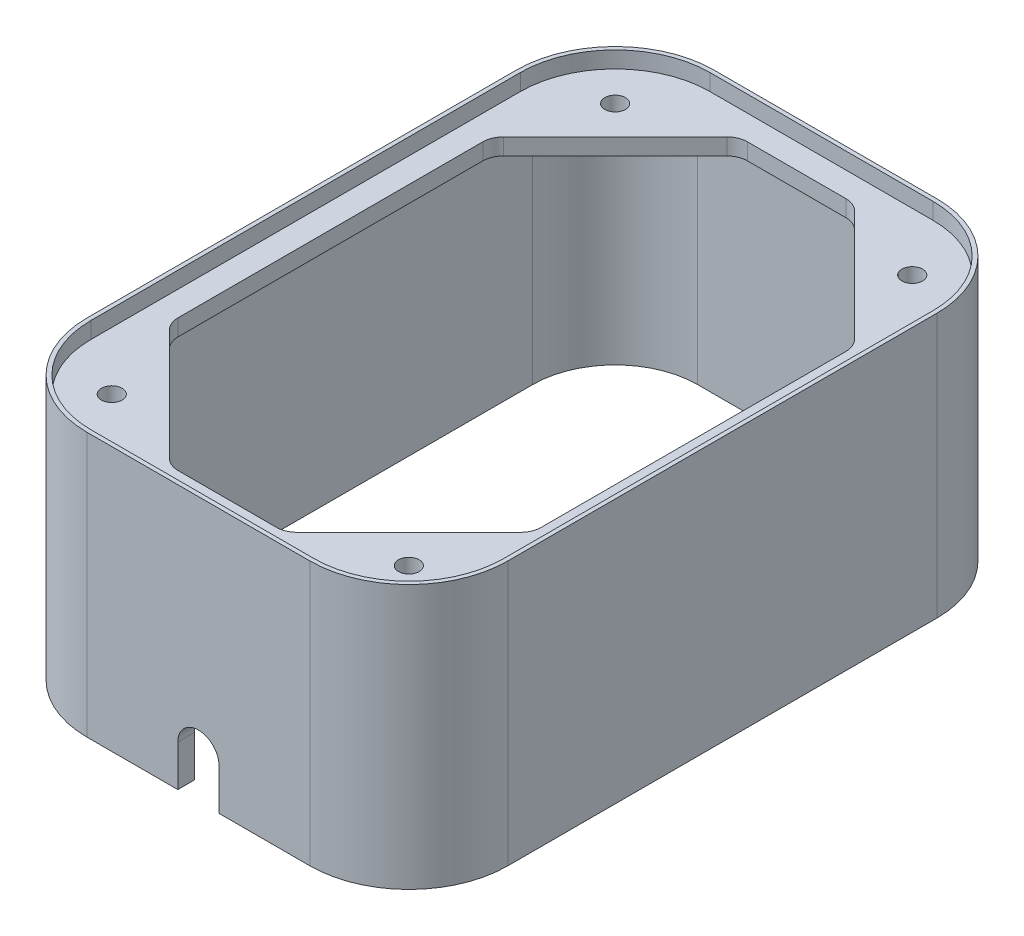
SolidWorks part; units mm, degrees
ref_plane "Front Plane" through (0, 0, 0) normal (0, 0, 1) x (1, 0, 0)
ref_plane "Top Plane" through (0, 0, 0) normal (0, 1, 0) x (1, 0, 0)
ref_plane "Right Plane" through (0, 0, 0) normal (1, 0, 0) x (0, 0, -1)
sketch "Sketch1" plane through (0, 0, 0) normal (0, 1, 0) x (1, 0, 0)
  line L0 (98.6595, -61) -> (-159.6366, -61) construction
  line L1 (-27, -75) -> (27, -75) construction
  line L2 (-50, -52) -> (-50, 52) construction
  line L3 (-27, 75) -> (27, 75) construction
  line L4 (50, -52) -> (50, 52) construction
  line L5 (-50, -75) -> (50, 75) construction
  line L6 (-50, 75) -> (50, -75) construction
  line L7 (-170.2562, 61) -> (110.7637, 61) construction
  line L8 (-36, 110.6206) -> (-36, -161.9524) construction
  line L9 (0, -145.8622) -> (0, 134.5406) construction
  line L10 (-51, -52) -> (-51, 52)
  line L15 (-27, 76) -> (27, 76)
  line L16 (51, -52) -> (51, 52)
  line L17 (-27, -76) -> (27, -76)
  line L22 (-44, -36.9289) -> (-44, 36.9289)
  line L23 (-11.9289, 69) -> (11.9289, 69)
  line L24 (44, -36.9289) -> (44, 36.9289)
  line L25 (-11.9289, -69) -> (11.9289, -69)
  line L26 (-15.4645, 67.5355) -> (-42.5355, 40.4645)
  line L27 (15.4645, 67.5355) -> (42.5355, 40.4645)
  line L28 (103.8586, 0) -> (-107.0383, 0) construction
  line L29 (15.4645, -67.5355) -> (42.5355, -40.4645)
  line L30 (-15.4645, -67.5355) -> (-42.5355, -40.4645)
  line L31 (14, 69) -> (27, 69) construction
  line L32 (-27, 69) -> (-14, 69) construction
  line L33 (-27, 69) -> (27, 69) construction
  line L34 (-44, 39) -> (-44, 52) construction
  line L35 (-44, -52) -> (-44, 52) construction
  line L36 (44, -52) -> (44, -39) construction
  line L37 (44, 39) -> (44, 52) construction
  line L38 (44, -52) -> (44, 52) construction
  line L39 (-27, -69) -> (-14, -69) construction
  line L40 (14, -69) -> (27, -69) construction
  line L41 (-27, -69) -> (27, -69) construction
  line L42 (-44, -52) -> (-44, -39) construction
  arc A0 (-27, -75) -> (-50, -52) centre (-27, -52) cw construction
  arc A1 (27, -75) -> (50, -52) centre (27, -52) ccw construction
  arc A2 (27, 75) -> (50, 52) centre (27, 52) cw construction
  arc A3 (-50, 52) -> (-27, 75) centre (-27, 52) cw construction
  circle A4 centre (-36, 61) radius 2.5
  circle A5 centre (-36, -61) radius 2.5
  circle A6 centre (36, -61) radius 2.5
  circle A7 centre (36, 61) radius 2.5
  arc A19 (-51, 52) -> (-27, 76) centre (-27, 52) cw
  arc A20 (27, 76) -> (51, 52) centre (27, 52) cw
  arc A21 (27, -76) -> (51, -52) centre (27, -52) ccw
  arc A22 (-27, -76) -> (-51, -52) centre (-27, -52) cw
  arc A23 (-41.4222, 61) -> (-41.0485, 61.5728) centre (-27, 52) cw construction
  arc A24 (41.4222, 61) -> (44, 52) centre (27, 52) cw construction
  arc A25 (41.4222, -61) -> (44, -52) centre (27, -52) ccw construction
  arc A26 (-41.4222, -61) -> (-44, -52) centre (-27, -52) cw construction
  arc A27 (-36, 66.4222) -> (-27, 69) centre (-27, 52) cw construction
  arc A28 (-44, 52) -> (-41.4222, 61) centre (-27, 52) cw construction
  arc A29 (-41.0485, 61.5728) -> (-36, 66.4222) centre (-27, 52) cw construction
  arc A30 (-44, 52) -> (-27, 69) centre (-27, 52) cw construction
  arc A31 (41.0485, 61.5728) -> (41.4222, 61) centre (27, 52) cw construction
  arc A32 (27, 69) -> (41.0485, 61.5728) centre (27, 52) cw construction
  arc A33 (27, 69) -> (44, 52) centre (27, 52) cw construction
  arc A34 (41.0485, -61.5728) -> (41.4222, -61) centre (27, -52) ccw construction
  arc A35 (27, -69) -> (41.0485, -61.5728) centre (27, -52) ccw construction
  arc A36 (27, -69) -> (44, -52) centre (27, -52) ccw construction
  arc A37 (-36, -66.4222) -> (-41.0485, -61.5728) centre (-27, -52) cw construction
  arc A38 (-27, -69) -> (-36, -66.4222) centre (-27, -52) cw construction
  arc A39 (-27, -69) -> (-44, -52) centre (-27, -52) cw construction
  arc A40 (-41.0485, -61.5728) -> (-41.4222, -61) centre (-27, -52) cw construction
  arc A41 (-42.5355, 40.4645) -> (-44, 36.9289) centre (-39, 36.9289) ccw
  arc A42 (-42.5355, -40.4645) -> (-44, -36.9289) centre (-39, -36.9289) cw
  arc A43 (-15.4645, -67.5355) -> (-11.9289, -69) centre (-11.9289, -64) ccw
  arc A44 (42.5355, 40.4645) -> (44, 36.9289) centre (39, 36.9289) cw
  arc A45 (42.5355, -40.4645) -> (44, -36.9289) centre (39, -36.9289) ccw
  arc A46 (15.4645, -67.5355) -> (11.9289, -69) centre (11.9289, -64) cw
  arc A47 (-15.4645, 67.5355) -> (-11.9289, 69) centre (-11.9289, 64) cw
  arc A48 (15.4645, 67.5355) -> (11.9289, 69) centre (11.9289, 64) ccw
  point P0 (0, 0)
  dimension "D3" = 23
  dimension "D7" = 5
  dimension "D9" = 7
  dimension "D11" = 30
  dimension "D13" = 5
  dimension "D1" = 150
  dimension "D2" = 100
  dimension "D4" = 14
  dimension "D5" = 14
  dimension "D6" = 14
  dimension "D8" = 1
  dimension "D10" = 45
  dimension "D12" = 30
extrude "Boss-Extrude1" add sketch "Sketch1" against normal blind 4
sketch "Sketch2" plane through (0, 0, 0) normal (0, 1, 0) x (1, 0, 0)
  line L0 (-27, -76) -> (27, -76) construction
  line L1 (51, -52) -> (51, 52) construction
  line L2 (27, 76) -> (-27, 76) construction
  line L3 (-51, 52) -> (-51, -52) construction
  line L4 (-27, -76) -> (27, -76)
  line L5 (51, -52) -> (51, 52)
  line L6 (27, 76) -> (-27, 76)
  line L7 (-51, 52) -> (-51, -52)
  line L8 (-50, 52) -> (-50, -52)
  line L9 (-27, -75) -> (27, -75)
  line L10 (50, -52) -> (50, 52)
  line L11 (27, 75) -> (-27, 75)
  arc A0 (-51, -52) -> (-27, -76) centre (-27, -52) ccw construction
  arc A1 (27, -76) -> (51, -52) centre (27, -52) ccw construction
  arc A2 (51, 52) -> (27, 76) centre (27, 52) ccw construction
  arc A3 (-27, 76) -> (-51, 52) centre (-27, 52) ccw construction
  arc A4 (-51, -52) -> (-27, -76) centre (-27, -52) ccw
  arc A5 (27, -76) -> (51, -52) centre (27, -52) ccw
  arc A6 (51, 52) -> (27, 76) centre (27, 52) ccw
  arc A7 (-27, 76) -> (-51, 52) centre (-27, 52) ccw
  arc A8 (-50, -52) -> (-27, -75) centre (-27, -52) ccw
  arc A9 (27, -75) -> (50, -52) centre (27, -52) ccw
  arc A10 (50, 52) -> (27, 75) centre (27, 52) ccw
  arc A11 (-27, 75) -> (-50, 52) centre (-27, 52) ccw
  dimension "D1" = 1
extrude "Boss-Extrude2" add sketch "Sketch2" along normal blind 4
sketch "Sketch3" plane through (0, -4, 0) normal (0, -1, 0) x (1, 0, 0)
  line L0 (-51, -52) -> (-51, 52) construction
  line L1 (27, -76) -> (-27, -76) construction
  line L2 (51, 52) -> (51, -52) construction
  line L3 (-27, 76) -> (27, 76) construction
  line L4 (-51, -52) -> (-51, 52)
  line L5 (27, -76) -> (-27, -76)
  line L6 (51, 52) -> (51, -52)
  line L7 (-27, 76) -> (27, 76)
  line L8 (-47, -52) -> (-47, 52)
  line L9 (-27, 72) -> (27, 72)
  line L10 (47, 52) -> (47, -52)
  line L11 (27, -72) -> (-27, -72)
  arc A0 (-51, -52) -> (-27, -76) centre (-27, -52) ccw construction
  arc A1 (27, -76) -> (51, -52) centre (27, -52) ccw construction
  arc A2 (51, 52) -> (27, 76) centre (27, 52) ccw construction
  arc A3 (-27, 76) -> (-51, 52) centre (-27, 52) ccw construction
  arc A4 (-51, -52) -> (-27, -76) centre (-27, -52) ccw
  arc A5 (27, -76) -> (51, -52) centre (27, -52) ccw
  arc A6 (51, 52) -> (27, 76) centre (27, 52) ccw
  arc A7 (-27, 76) -> (-51, 52) centre (-27, 52) ccw
  arc A8 (-27, 72) -> (-47, 52) centre (-27, 52) ccw
  arc A9 (47, 52) -> (27, 72) centre (27, 52) ccw
  arc A10 (27, -72) -> (47, -52) centre (27, -52) ccw
  arc A11 (-47, -52) -> (-27, -72) centre (-27, -52) ccw
  dimension "D1" = 4
extrude "Boss-Extrude3" add sketch "Sketch3" along normal blind 56
sketch "Sketch4" plane through (0, 0, 76) normal (0, 0, 1) x (1, 0, 0)
  line L0 (27, -60) -> (-27, -60) construction
  line L1 (5, -60) -> (-5, -60)
  line L2 (0, -72.0666) -> (0, 7.863) construction
  line L3 (5, -50) -> (5, -60)
  line L4 (-5, -50) -> (-5, -60)
  line L5 (-5, -60) -> (-27, -60) construction
  line L6 (27, -60) -> (5, -60) construction
  arc A0 (5, -50) -> (-5, -50) centre (0, -50) ccw
  arc A1 (0, -55) -> (5, -50) centre (0, -50) ccw construction
  arc A2 (-5, -50) -> (0, -55) centre (0, -50) ccw construction
  dimension "D1" = 10
  dimension "D2" = 10
extrude "Cut-Extrude1" cut sketch "Sketch4" against normal up to next
fillet "Fillet1" radius 2 8 edges at (-41.1421, -4, 66.1421) (0, -4, 72) (41.1421, -4, 66.1421) (47, -4, 0) (41.1421, -4, -66.1421) (0, -4, -72) (-41.1421, -4, -66.1421) (-47, -4, 0)
